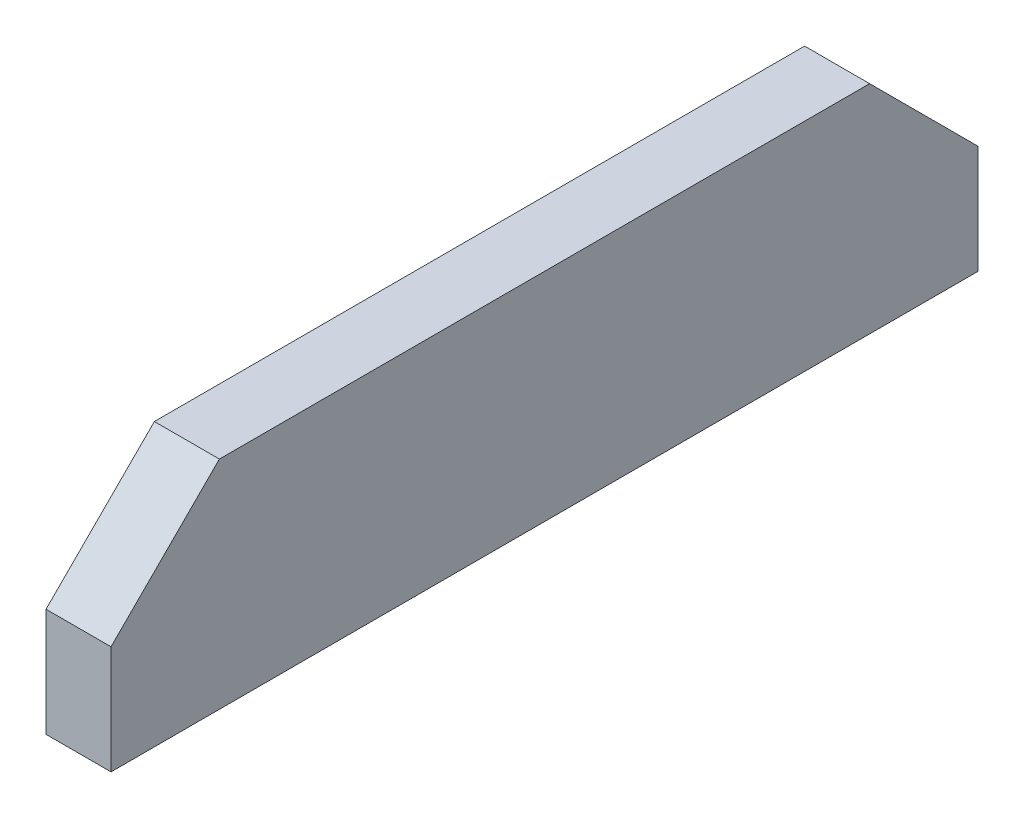
SolidWorks part; units mm, degrees
ref_plane "Спереди" through (0, 0, 0) normal (0, 0, 1) x (1, 0, 0)
ref_plane "Сверху" through (0, 0, 0) normal (0, 1, 0) x (1, 0, 0)
ref_plane "Справа" through (0, 0, 0) normal (1, 0, 0) x (0, 0, -1)
sketch "Эскиз1" plane through (0, 0, 0) normal (1, 0, 0) x (0, 0, -1)
  line L0 (0, 0) -> (40, 0)
  line L1 (40, 0) -> (40, 5)
  line L2 (40, 5) -> (35, 10)
  line L3 (35, 10) -> (5, 10)
  line L4 (5, 10) -> (0, 5)
  line L5 (0, 5) -> (0, 0)
extrude "Бобышка-Вытянуть1" add sketch "Эскиз1" along normal blind 3
